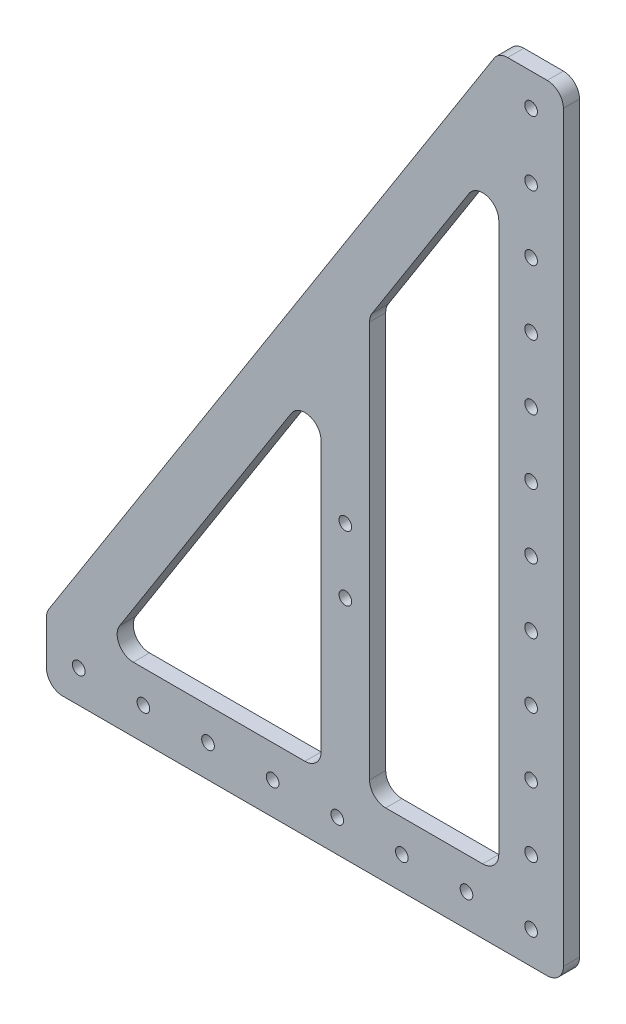
SolidWorks part; units mm, degrees
material "6061-T6 (SS)"
ref_plane "Front Plane" through (0, 0, 0) normal (0, 0, 1) x (1, 0, 0)
ref_plane "Top Plane" through (0, 0, 0) normal (0, 1, 0) x (1, 0, 0)
ref_plane "Right Plane" through (0, 0, 0) normal (1, 0, 0) x (0, 0, -1)
sketch "Sketch1" plane through (0, 0, 0) normal (0, 0, 1) x (1, 0, 0)
  line L0 (0, 25.4) -> (177.8, 304.8)
  line L1 (177.8, 304.8) -> (203.2, 304.8)
  line L2 (0, 25.4) -> (0, 0)
  line L3 (0, 0) -> (203.2, 0)
  line L4 (203.2, 304.8) -> (203.2, 0)
  dimension "D1" = 304.8
  dimension "D2" = 203.2
  dimension "D3" = 25.4
  dimension "D4" = 25.4
extrude "Boss-Extrude1" add sketch "Sketch1" along normal blind 6.35
sketch "Sketch2" plane through (0, 0, 6.35) normal (0, 0, 1) x (1, 0, 0)
  line L0 (0, 0) -> (203.2, 0) construction
  line L1 (203.2, 0) -> (203.2, 304.8) construction
  line L2 (22.5801, 25.4) -> (177.8, 25.4)
  line L3 (177.8, 25.4) -> (177.8, 269.3169)
  line L4 (177.8, 269.3169) -> (22.5801, 25.4)
  line L5 (177.8, 304.8) -> (0, 25.4) construction
  circle A0 centre (190.5, 12.7) radius 2.4892
  circle A1 centre (165.1, 12.7) radius 2.4892
  circle A2 centre (139.7, 12.7) radius 2.4892
  circle A3 centre (114.3, 12.7) radius 2.4892
  circle A4 centre (88.9, 12.7) radius 2.4892
  circle A5 centre (63.5, 12.7) radius 2.4892
  circle A6 centre (38.1, 12.7) radius 2.4892
  circle A67 centre (190.5, 38.1) radius 2.4892
  circle A68 centre (190.5, 63.5) radius 2.4892
  circle A69 centre (190.5, 88.9) radius 2.4892
  circle A70 centre (190.5, 114.3) radius 2.4892
  circle A71 centre (190.5, 139.7) radius 2.4892
  circle A72 centre (190.5, 165.1) radius 2.4892
  circle A73 centre (190.5, 190.5) radius 2.4892
  circle A74 centre (190.5, 215.9) radius 2.4892
  circle A75 centre (190.5, 241.3) radius 2.4892
  circle A76 centre (190.5, 266.7) radius 2.4892
  circle A161 centre (190.5, 292.1) radius 2.4892
  circle A233 centre (139.7, 38.1) radius 2.4892 construction
  circle A234 centre (114.3, 38.1) radius 2.4892 construction
  circle A235 centre (88.9, 38.1) radius 2.4892 construction
  circle A236 centre (63.5, 38.1) radius 2.4892 construction
  circle A237 centre (38.1, 38.1) radius 2.4892 construction
  circle A238 centre (165.1, 63.5) radius 2.4892 construction
  circle A239 centre (139.7, 63.5) radius 2.4892 construction
  circle A240 centre (114.3, 63.5) radius 2.4892 construction
  circle A241 centre (88.9, 63.5) radius 2.4892 construction
  circle A242 centre (63.5, 63.5) radius 2.4892 construction
  circle A243 centre (38.1, 63.5) radius 2.4892 construction
  circle A244 centre (165.1, 88.9) radius 2.4892 construction
  circle A245 centre (139.7, 88.9) radius 2.4892 construction
  circle A246 centre (114.3, 88.9) radius 2.4892 construction
  circle A247 centre (88.9, 88.9) radius 2.4892 construction
  circle A248 centre (63.5, 88.9) radius 2.4892 construction
  circle A249 centre (38.1, 88.9) radius 2.4892 construction
  circle A250 centre (165.1, 114.3) radius 2.4892 construction
  circle A251 centre (139.7, 114.3) radius 2.4892 construction
  circle A252 centre (114.3, 114.3) radius 2.4892 construction
  circle A253 centre (88.9, 114.3) radius 2.4892 construction
  circle A254 centre (63.5, 114.3) radius 2.4892 construction
  circle A255 centre (38.1, 114.3) radius 2.4892 construction
  circle A256 centre (165.1, 139.7) radius 2.4892 construction
  circle A257 centre (139.7, 139.7) radius 2.4892 construction
  circle A258 centre (114.3, 139.7) radius 2.4892 construction
  circle A259 centre (88.9, 139.7) radius 2.4892 construction
  circle A260 centre (63.5, 139.7) radius 2.4892 construction
  circle A261 centre (38.1, 139.7) radius 2.4892 construction
  circle A262 centre (165.1, 165.1) radius 2.4892 construction
  circle A263 centre (139.7, 165.1) radius 2.4892 construction
  circle A264 centre (114.3, 165.1) radius 2.4892 construction
  circle A265 centre (88.9, 165.1) radius 2.4892 construction
  circle A266 centre (63.5, 165.1) radius 2.4892 construction
  circle A267 centre (38.1, 165.1) radius 2.4892 construction
  circle A268 centre (165.1, 190.5) radius 2.4892 construction
  circle A269 centre (139.7, 190.5) radius 2.4892 construction
  circle A270 centre (114.3, 190.5) radius 2.4892 construction
  circle A271 centre (88.9, 190.5) radius 2.4892 construction
  circle A272 centre (63.5, 190.5) radius 2.4892 construction
  circle A273 centre (38.1, 190.5) radius 2.4892 construction
  circle A274 centre (165.1, 215.9) radius 2.4892 construction
  circle A275 centre (139.7, 215.9) radius 2.4892 construction
  circle A276 centre (114.3, 215.9) radius 2.4892 construction
  circle A277 centre (88.9, 215.9) radius 2.4892 construction
  circle A278 centre (63.5, 215.9) radius 2.4892 construction
  circle A279 centre (38.1, 215.9) radius 2.4892 construction
  circle A280 centre (165.1, 241.3) radius 2.4892 construction
  circle A281 centre (139.7, 241.3) radius 2.4892 construction
  circle A282 centre (114.3, 241.3) radius 2.4892 construction
  circle A283 centre (88.9, 241.3) radius 2.4892 construction
  circle A284 centre (63.5, 241.3) radius 2.4892 construction
  circle A285 centre (38.1, 241.3) radius 2.4892 construction
  circle A286 centre (165.1, 266.7) radius 2.4892 construction
  circle A287 centre (139.7, 266.7) radius 2.4892 construction
  circle A288 centre (114.3, 266.7) radius 2.4892 construction
  circle A289 centre (88.9, 266.7) radius 2.4892 construction
  circle A290 centre (63.5, 266.7) radius 2.4892 construction
  circle A291 centre (38.1, 266.7) radius 2.4892 construction
  circle A292 centre (165.1, 38.1) radius 2.4892 construction
  circle A293 centre (12.7, 12.7) radius 2.4892
  circle A477 centre (12.7, 38.1) radius 2.4892 [skipped]
  circle A485 centre (12.7, 63.5) radius 2.4892 [skipped]
  circle A493 centre (12.7, 88.9) radius 2.4892 [skipped]
  circle A501 centre (12.7, 114.3) radius 2.4892 [skipped]
  circle A509 centre (12.7, 139.7) radius 2.4892 [skipped]
  circle A517 centre (12.7, 165.1) radius 2.4892 [skipped]
  circle A525 centre (12.7, 190.5) radius 2.4892 [skipped]
  circle A533 centre (12.7, 215.9) radius 2.4892 [skipped]
  circle A541 centre (12.7, 241.3) radius 2.4892 [skipped]
  circle A549 centre (12.7, 266.7) radius 2.4892 [skipped]
  circle A557 centre (165.1, 292.1) radius 2.4892 [skipped]
  circle A558 centre (139.7, 292.1) radius 2.4892 [skipped]
  circle A559 centre (114.3, 292.1) radius 2.4892 [skipped]
  circle A560 centre (88.9, 292.1) radius 2.4892 [skipped]
  circle A561 centre (63.5, 292.1) radius 2.4892 [skipped]
  circle A562 centre (38.1, 292.1) radius 2.4892 [skipped]
  circle A563 centre (12.7, 292.1) radius 2.4892 [skipped]
  dimension "D1" = 12.7
  dimension "D2" = 12.7
  dimension "D3" = 4.9784
  dimension "D6" = 25.4
  dimension "D7" = 25.4
  dimension "D8" = 25.4
  dimension "D9" = 25.4
  dimension "D10" = 19.05
  dimension "D5" = 8
  dimension "D4" = 12
extrude "Cut-Extrude1" cut sketch "Sketch2" against normal through all
sketch "Sketch4" plane through (0, 0, 0) normal (0, 0, -1) x (-1, 0, 0)
  line L0 (-107.95, 159.5526) -> (-107.95, 25.4)
  line L1 (-177.8, 269.3169) -> (-22.5801, 25.4) construction
  line L2 (-22.5801, 25.4) -> (-177.8, 25.4) construction
  line L3 (-127, 25.4) -> (-127, 189.4883)
  line L4 (-177.8, 25.4) -> (-177.8, 269.3169) construction
  line L5 (-22.5801, 25.4) -> (-177.8, 25.4) construction
  line L6 (-177.8, 269.3169) -> (-22.5801, 25.4) construction
  line L7 (-177.8, 269.3169) -> (-22.5801, 25.4)
  line L8 (-22.5801, 25.4) -> (-177.8, 25.4)
  circle A0 centre (-117.475, 114.3) radius 2.4892
  circle A1 centre (-117.475, 88.9) radius 2.4892
  point P14 (0, 0)
  line M7 (-22.5801, 25.4) -> (-177.8, 25.4)
  line M11 (-177.8, 269.3169) -> (-22.5801, 25.4)
  dimension "D4" = 4.9784
  dimension "D1" = 19.05
  dimension "D2" = 50.8
  dimension "D3" = 9.525
  dimension "D5" = 25.4
  dimension "D6" = 63.5
extrude "Boss-Extrude2" add sketch "Sketch4" against normal up to surface (6.35 mm away) contours L3 L0 A1 A0 M7 M11 up to face at (15.1892, 12.7, 6.35)
fillet "Fillet1" radius 6.35 12 edges at (203.2, 0, 3.175) (0, 25.4, 3.175) (177.8, 304.8, 3.175) (203.2, 304.8, 3.175) (0, 0, 3.175) (177.8, 25.4, 3.175) (177.8, 269.3169, 3.175) (22.5801, 25.4, 3.175) (127, 189.4883, 3.175) (127, 25.4, 3.175) (107.95, 159.5526, 3.175) (107.95, 25.4, 3.175)
